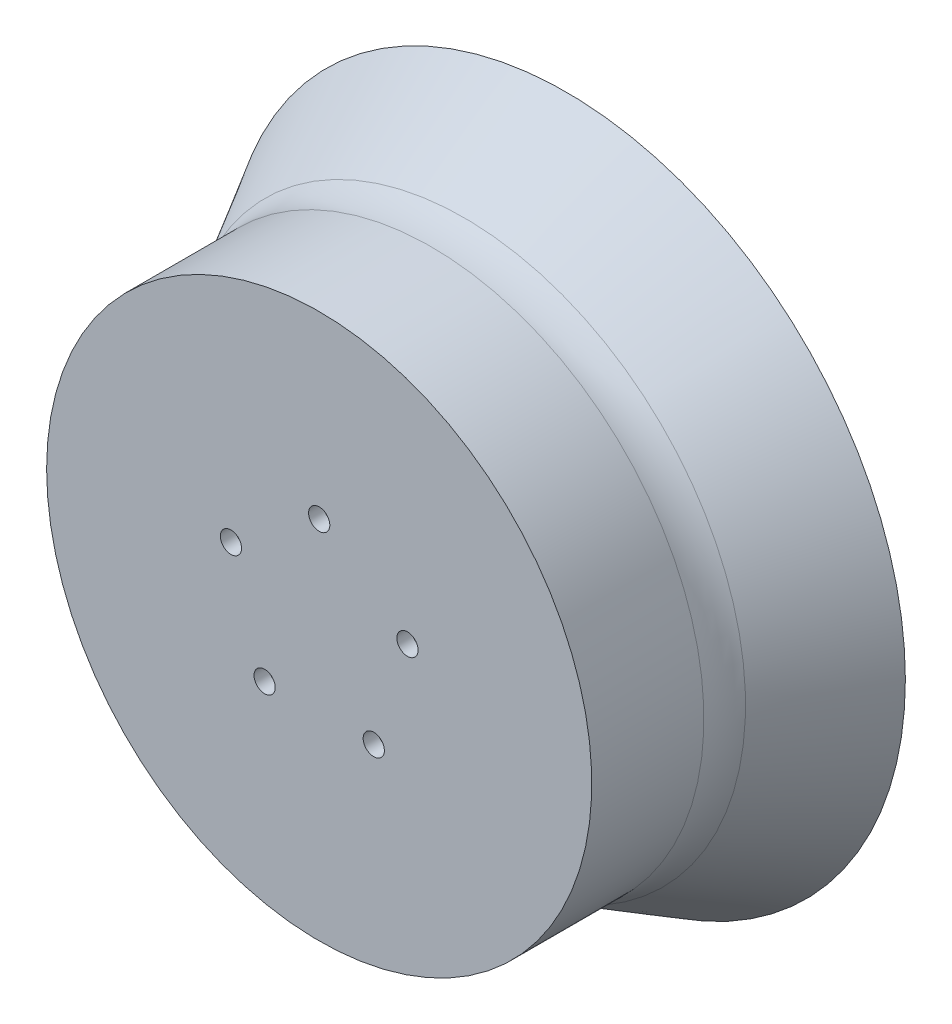
SolidWorks part; units mm, degrees
ref_plane "Front Plane" through (0, 0, 0) normal (0, 0, 1) x (1, 0, 0)
ref_plane "Top Plane" through (0, 0, 0) normal (0, 1, 0) x (1, 0, 0)
ref_plane "Right Plane" through (0, 0, 0) normal (1, 0, 0) x (0, 0, -1)
sketch "Sketch1" plane through (0, 0, 0) normal (0, 1, 0) x (1, 0, 0)
  line L0 (-44.45, -25.4) -> (44.45, -25.4) construction
  line L1 (7.9629, -25.4) -> (44.45, -25.4)
  line L2 (0, 0) -> (0, -35.687) construction
  line L3 (44.45, 0) -> (-44.45, 0) construction
  line L4 (44.45, -25.4) -> (44.45, 0)
  line L5 (44.45, -25.4) -> (44.45, 0) construction
  line L6 (0, -15.24) -> (0, -27.94)
  line L7 (0, -27.94) -> (46.99, -27.94)
  line L8 (46.99, -27.94) -> (46.99, -8.6126)
  line L9 (44.45, 0) -> (46.99, 0)
  line L10 (46.99, 0) -> (58.4734, 14.634)
  line L11 (58.4734, 14.634) -> (48.4889, -2.94)
  line L12 (5.4229, -15.24) -> (0, -15.24)
  line L13 (7.9629, -17.78) -> (7.9629, -15.24) construction
  line L14 (7.9629, -25.4) -> (7.9629, -17.78)
  line L15 (7.9629, -15.24) -> (5.4229, -15.24) construction
  line L19 (5.4229, -15.24) -> (7.9629, -17.78)
  arc A0 (46.99, -8.6126) -> (48.4889, -2.94) centre (58.4734, -8.6126) cw
  point P20 (8.1279, -17.5273)
  point P22 (5.9615, -15.24)
  point P23 (8.0333, -25.4)
  point P25 (5.695, -15.24)
  point P26 (7.9629, -17.6948)
  point P27 (0, -15.2955)
  point P28 (5.3421, -15.2126)
  dimension "D3" = 11.4834
  dimension "D7" = 2.54
  dimension "D1" = 2.54
  dimension "D2" = 2.54
  dimension "D4" = 2.94
  dimension "D5" = 45
  dimension "D6" = 12.7
revolve "Revolve1" add sketch "Sketch1" angle 360 about L2
sketch "Sketch2" plane through (0, 0, 27.94) normal (0, 0, 1) x (1, 0, 0)
  circle A0 centre (0, 16) radius 3.556
  circle A1 centre (0, 16) radius 1.8288
  circle A2 centre (0, 16) radius 1.8288
  circle A3 centre (15.2169, 4.9443) radius 1.8288
  circle A4 centre (15.2169, 4.9443) radius 1.8288
  circle A5 centre (9.4046, -12.9443) radius 1.8288
  circle A6 centre (9.4046, -12.9443) radius 1.8288
  circle A7 centre (-9.4046, -12.9443) radius 1.8288
  circle A8 centre (-9.4046, -12.9443) radius 1.8288
  circle A9 centre (-15.2169, 4.9443) radius 1.8288
  circle A10 centre (-15.2169, 4.9443) radius 1.8288
  circle A11 centre (15.2169, 4.9443) radius 3.556
  circle A12 centre (9.4046, -12.9443) radius 3.556
  circle A13 centre (-9.4046, -12.9443) radius 3.556
  circle A14 centre (-15.2169, 4.9443) radius 3.556
  dimension "D6" = 7.112
  dimension "D1" = 0
  dimension "D2" = 0
  dimension "D3" = 0
  dimension "D4" = 0
  dimension "D5" = 0
extrude "Cut-Extrude1" cut sketch "Sketch2" against normal through all contours A10 | A2 | A8 | A6 | A4
